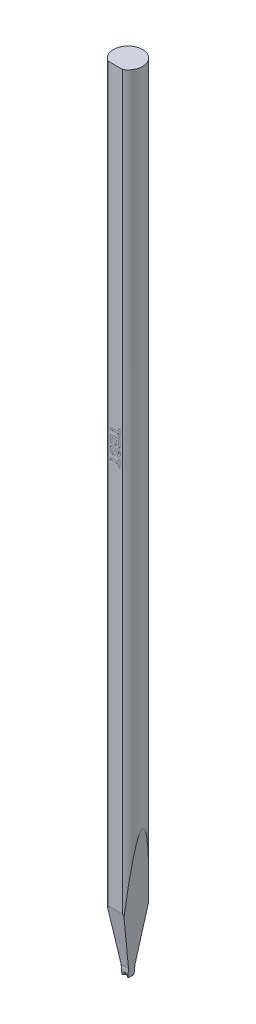
SolidWorks part; units mm, degrees
ref_plane "Ebene vorne" through (0, 0, 0) normal (0, 0, 1) x (1, 0, 0)
ref_plane "Ebene oben" through (0, 0, 0) normal (0, 1, 0) x (1, 0, 0)
ref_plane "Ebene rechts" through (0, 0, 0) normal (1, 0, 0) x (0, 0, -1)
sketch "sketch_TL_cutting" plane through (0, 0, 0) normal (0, 1, 0) x (1, 0, 0)
  circle A0 centre (0, 0) radius 1.4986
extrude "TL_cutting" add sketch "sketch_TL_cutting" along normal blind 81.28
sketch "sketch_TDF_grinding" plane through (0, 0, 0) normal (0, 1, 0) x (1, 0, 0)
  line L0 (0, 0) -> (0, -1.2954) construction
  line L1 (-1.5086, -4.3126) -> (1.5086, -4.3126)
  line L2 (-1.5086, -4.3126) -> (-1.5086, -1.2954)
  line L3 (-1.5086, -1.2954) -> (1.5086, -1.2954)
  line L4 (1.5086, -4.3126) -> (1.5086, -1.2954)
  circle A1 centre (0, 0) radius 1.4986 construction
  point P9 (0, -4.3126)
  dimension "TD_2Offset_X" = 3.0172
  dimension "TD_2Offset_Z" = 3.0172
extrude "TDF_grinding" cut sketch "sketch_TDF_grinding" along normal through all
sketch "sketch_engraving" plane through (0, 0, 1.2954) normal (0, 0, 1) x (1, 0, 0)
  line L0 (0.7535, 81.28) -> (-0.7535, 81.28) construction
  line L6 (-0.7535, 0) -> (0.7535, 0) construction
  line L7 (0, 0) -> (0, 49.28) construction
  line L8 (-0.5, 49.28) -> (-0.5, 0) construction
  text T0 "TEST" font "Arial" height 1
  dimension "D2" = 0.5
  dimension "EngravingStart" = 32
extrude "engraving" cut sketch "sketch_engraving" against normal blind 0.005
sketch "sketch_VW_VR_grinding" plane through (0, 0, 0) normal (0, 0, 1) x (1, 0, 0)
  line L0 (-1.4936, -0.01) -> (-1.4936, 0.874)
  line L1 (1.4936, -0.01) -> (1.4936, 0.874)
  line L2 (-1.4936, 0) -> (1.4936, 0) construction
  line L3 (-1.5086, 0.879) -> (-1.4986, 0.879)
  line L4 (1.4986, 0.879) -> (1.5086, 0.879)
  line L5 (-1.5086, 0.879) -> (-1.5086, -0.01)
  line L6 (-1.5086, -0.01) -> (-1.4936, -0.01)
  line L7 (1.4936, -0.01) -> (1.5086, -0.01)
  line L8 (1.5086, -0.01) -> (1.5086, 0.879)
  line L9 (-1.4986, 0.879) -> (-1.4986, 0.874) construction
  line L10 (-1.4936, 0.874) -> (-1.4986, 0.874) construction
  line L11 (1.4936, 0.874) -> (1.4986, 0.874) construction
  line L12 (1.4986, 0.879) -> (1.4986, 0.874) construction
  arc A0 (-1.4986, 0.879) -> (-1.4936, 0.874) centre (-1.4986, 0.874) cw
  arc A2 (1.4936, 0.874) -> (1.4986, 0.879) centre (1.4986, 0.874) cw
  dimension "D1" = 0.01
  dimension "D4" = 3.0172
extrude "VW_VR_grinding" cut sketch "sketch_VW_VR_grinding" against normal blind 1.5086 and the other way blind 1.5086
sketch "sketch_ISA_grinding" plane through (0, 0, 0) normal (0, 0, 1) x (1, 0, 0)
  line L0 (-0.2997, 0) -> (-1.5086, 13.8176)
  line L4 (1.5086, 13.8176) -> (0.2997, 0)
  line L5 (0.2997, 0) -> (-0.2997, 0)
  line L6 (0, 0) -> (0, 30.49) construction
  line L7 (-1.5086, 13.8176) -> (-1.5086, -0.01)
  line L12 (-1.5086, -0.01) -> (1.5086, -0.01)
  line L13 (1.5086, -0.01) -> (1.5086, 13.8176)
  dimension "ISA" = 10
  dimension "TD_2Offset" = 3.0172
  dimension "Offset" = 0.01
extrude "ISA_grinding" cut sketch "sketch_ISA_grinding" against normal blind 1.5086 and the other way blind 1.5086
sketch "sketch_pre_FRX_BRX" plane through (0, 0, 0) normal (1, 0, 0) x (0, 0, -1)
  line L0 (1.4986, -0.01) -> (1.4986, 3.9152) construction
  line L1 (-1.2954, -0.01) -> (-1.2954, 0.879) construction
  line L2 (-0.3251, -0.01) -> (-0.3251, 0.879)
  line L3 (-0.3251, 0.879) -> (-1.5086, 0.879)
  line L4 (-1.5086, 0.879) -> (-1.5086, -0.01)
  line L5 (-1.5086, -0.01) -> (-0.3251, -0.01)
  line L6 (0.3251, -0.01) -> (0.3251, 0.879)
  line L7 (0.3251, 0.879) -> (1.5086, 0.879)
  line L8 (1.5086, 0.879) -> (1.5086, -0.01)
  line L9 (1.5086, -0.01) -> (0.3251, -0.01)
  dimension "D3" = 0.01
  dimension "D4" = 0.889
  dimension "D5" = 3.0172
  dimension "D6" = 0.6502
  dimension "D2" = 0.01
  dimension "D7" = 1.8237
extrude "pre_FRX_BRX" cut sketch "sketch_pre_FRX_BRX" against normal blind 1.5086 and the other way blind 1.5086
sketch "sketch_contour_V-Groove" plane through (0, 0, 0) normal (1, 0, 0) x (0, 0, -1)
  line L0 (-1.2954, 0.1905) -> (0, 0.1905)
  line L1 (0, 0.1905) -> (1.4986, 0.1905)
  line L2 (1.4986, -0.8411) -> (1.4986, 1.3178) construction
  line L3 (-1.2954, -0.9209) -> (-1.2954, 1.9363) construction
  line L4 (-1.2954, 0) -> (1.4986, 0) construction
  line L5 (0.3251, 0) -> (0.3251, 0.1905) construction
  line L6 (-0.3251, 0) -> (-0.3251, 0.1905) construction
  dimension "D1" = 0
ref_plane "front" through (0, 0, 1.2954) normal (0, 0, 1) x (1, 0, 0)
ref_plane "back" through (0, 0, -1.4986) normal (0, 0, 1) x (1, 0, 0)
sketch "sketch_section_V-Groove" plane through (0, 0, 1.2954) normal (0, 0, 1) x (1, 0, 0)
  line L0 (-1.499, -1.905) -> (-0.0499, 0.1645)
  line L2 (0.0499, 0.1645) -> (1.499, -1.905)
  line L3 (-1.499, -1.905) -> (1.499, -1.905)
  line L4 (0, -1.905) -> (0, 0.1905) construction
  line L5 (-0.1651, 0) -> (0.1651, 0) construction
  line L6 (-0.2997, 0) -> (0.2997, 0) construction
  arc A0 (0.0499, 0.1645) -> (-0.0499, 0.1645) centre (0, 0.1296) ccw
  point P5 (0, 0)
  point P9 (0, 0)
  point P14 (0, 0)
  point P15 (0, 0)
  point P16 (0, 0)
  point P17 (0, 0)
  dimension "GA" = 70
sweep "V-Groove_EDM" cut profiles "sketch_section_V-Groove" path "sketch_contour_V-Groove"
fillet "FR_EDM" radius 0.2261 3 edges at (0.1075, 0.0823, 0.3251) (0, 0.1905, 0.3251) (-0.1075, 0.0823, 0.3251)
fillet "BR_EDM" radius 0.2261 3 edges at (0.1075, 0.0823, -0.3251) (0, 0.1905, -0.3251) (-0.1075, 0.0823, -0.3251)
sketch "sketch_FA_BA_grinding" plane through (0, 0, 0) normal (1, 0, 0) x (0, 0, -1)
  line L2 (2.4986, 13.2154) -> (2.4986, -0.1)
  line L3 (2.4986, -0.1) -> (0.3251, -0.1)
  line L5 (0.3251, -0.1) -> (0.3251, 0.889)
  line L6 (0.3251, 0.889) -> (2.4986, 13.2154)
  line L7 (1.4986, -0.1) -> (1.4986, 7.5441) construction
  line L8 (-1.2954, 6.3917) -> (-1.2954, -0.1) construction
  line L9 (-4.003, 21.7474) -> (-0.3251, 0.889)
  line L10 (-0.3251, 0.889) -> (-0.3251, -0.1)
  line L11 (-0.3251, -0.1) -> (-4.003, -0.1)
  line L12 (-4.003, -0.1) -> (-4.003, 21.7474)
  line L13 (-0.3251, 0.889) -> (0.3251, 0.889) construction
  dimension "D4" = 1
  dimension "D1" = 0.1
  dimension "FA" = 10
  dimension "BA" = 10
extrude "FA_BA_grinding" cut sketch "sketch_FA_BA_grinding" against normal blind 1.5086 and the other way blind 1.5086
sketch "sketch_groove_dimensions" plane through (0, 0, 0) normal (1, 0, 0) x (0, 0, -1)
  line L0 (-0.0991, 0.1905) -> (0.0991, 0.1905)
  line L1 (-0.3251, 0) -> (-0.3251, 0.4166) construction
  line L2 (1.4986, 0) -> (1.4986, 0.4166) construction
  line L3 (0.3251, 0) -> (0.3251, 0.4166) construction
  line L4 (-1.2954, 0) -> (-1.2954, 0.3999) construction
  arc A0 (0.0991, 0.1905) -> (0.3251, 0.4166) centre (0.0991, 0.4166) ccw
  arc A1 (-0.0991, 0.1905) -> (-0.3251, 0.4166) centre (-0.0991, 0.4166) cw
equation "\"_Offset\"=0.01mm"
equation "\"TL\"=81.28mm"
equation "\"TD\"=2.9972mm"
equation "\"TDF\"=2.794mm"
equation "\"BA\"=10deg"
equation "\"ISA\"=10deg"
equation "\"FA\"=10deg"
equation "\"GR\"=0.06096mm"
equation "\"GA\"=70deg"
equation "\"GD\"=0.1905mm"
equation "\"FL\"=0.65024mm"
equation "\"F\"=0.35052mm"
equation "\"FX\"=0mm"
equation "\"B\"=0.3302mm"
equation "\"VW\"=0mm"
equation "\"cleaned_VR\"= IIF ( \"VR\" > 0 , \"VR\" , \"E\" - \"_Offset\" )"
equation "\"cleaned_VW\"= IIF ( \"VW\" > 0 , \"VW\" , \"TD\" - \"_Offset\" )"
equation "\"back_edge\"= \"TD\" / 2 - \"X\""
equation "\"side_edge_Offset\"= \"TD\" / 2 + \"_Offset\""
equation "\"TD@sketch_TL_cutting\"=\"TD\""
equation "\"TL@TL_cutting\"=\"TL\""
equation "\"TDF@sketch_TDF_grinding\"=\"TDF\""
equation "\"TD_2Offset_X@sketch_TDF_grinding\"=\"TD\"+2*\"_Offset\""
equation "\"TD_2Offset_Z@sketch_TDF_grinding\"=\"TD\"+2*\"_Offset\""
equation "\"TL_Offset\"= \"TL\" + \"_Offset\""
equation "\"ISA@sketch_ISA_grinding\"=\"ISA\""
equation "\"W@sketch_ISA_grinding\"=\"W\""
equation "\"TD_2Offset@sketch_ISA_grinding\"=\"TD\"+2*\"_Offset\""
equation "\"Offset@sketch_ISA_grinding\"=\"_Offset\""
equation "\"05TD_Offset_posZ@ISA_grinding\"=\"side_edge_Offset\""
equation "\"05TD_Offset_negZ@ISA_grinding\"=\"side_edge_Offset\""
equation "\"E\"=0.889mm"
equation "\"cleaned_X\"= IIF ( \"X\" > 0 , \"X\" , \"TD\" / 2 - \"FL\" / 2 )"
equation "\"FR\"=0.22606mm"
equation "\"BR\"=0.22606mm"
equation "\"D1\"= \"side_edge_Offset\""
equation "\"D2\"= \"side_edge_Offset\""
equation "\"TDF@sketch_FA_BA_grinding\" = \"TDF\""
equation "\"FL@sketch_FA_BA_grinding\"=\"FL\""
equation "\"E@sketch_FA_BA_grinding\" = \"E\""
equation "\"D1@FA_BA_grinding\"=\"side_edge_Offset\""
equation "\"D2@FA_BA_grinding\"=\"side_angle_Offset\""
equation "\"10GD@sketch_section_V-Groove\" = 10 * \"GD\""
equation "\"GA@sketch_section_V-Groove\" = \"GA\""
equation "\"B@sketch_section_V-Groove\" = \"B\""
equation "\"GD@sketch_contour_V-Groove\" = \"GD\""
equation "\"cleaned_FRX\"= IIF ( \"FRX\" > 0 , \"FRX\" , \"FR\" )"
equation "\"cleaned_BRX\"= IIF ( \"BRX\" > 0 , \"BRX\" , \"BR\" )"
equation "\"FL_groove_angle\"=0deg"
equation "\"D3@sketch_pre_FRX_BRX\" = \"_Offset\""
equation "\"D4@sketch_pre_FRX_BRX\" = \"E\""
equation "\"D5@sketch_pre_FRX_BRX\" = 2 * \"side_edge_Offset\""
equation "\"D6@sketch_pre_FRX_BRX\" = \"FL\" + ( \"FR\" - \"cleaned_FRX\" ) + ( \"BR\" - \"cleaned_BRX\" )"
equation "\"TD/2@sketch_pre_FRX_BRX\" = \"TD\" / 2"
equation "\"TDF@sketch_pre_FRX_BRX\" = \"TDF\""
equation "\"D2@sketch_pre_FRX_BRX\" = \"_Offset\""
equation "\"D1@pre_FRX_BRX\" = \"side_edge_Offset\""
equation "\"D2@pre_FRX_BRX\" = \"side_edge_Offset\""
equation "\"D1@BR_EDM\"=\"BR\""
equation "\"TD/2@sketch_FA_BA_grinding\" = \"TD\" / 2"
equation "\"TD/2@sketch_contour_V-Groove\" = \"TD\" / 2"
equation "\"TDF@sketch_contour_V-Groove\" = \"TDF\""
equation "\"D1@sketch_contour_V-Groove\"=\"FL_groove_angle\""
equation "\"FL@sketch_contour_V-Groove\"=\"FL\""
equation "\"FL/2@sketch_contour_V-Groove\" = \"FL\" / 2"
equation "\"D1@FR_EDM\"=\"FR\""
equation "\"D1@sketch_VW_VR_grinding\" = \"_Offset\""
equation "\"D4@sketch_VW_VR_grinding\" = 2 * \"side_edge_Offset\""
equation "\"VR@sketch_VW_VR_grinding\" = \"cleaned_VR\""
equation "\"VW@sketch_VW_VR_grinding\"=\"cleaned_VW\""
equation "\"D1@VW_VR_grinding\" = \"side_edge_Offset\""
equation "\"D2@VW_VR_grinding\" = \"side_edge_Offset\""
equation "\"X\"=0mm"
equation "\"VR\"=0mm"
equation "\"W\"=0.59944mm"
equation "\"VW_radius\"= \"cleaned_VW\" / 10"
equation "\"VW_radius_cleaned\"= IIF ( \"VW\" > 0 , \"VW_radius\" , \"_Offset\" / 2 )"
equation "\"D2@sketch_VW_VR_grinding\"=\"VW_radius_cleaned\""
equation "\"FRX\"=0mm"
equation "\"BRX\"=0mm"
equation "\"FA@sketch_FA_BA_grinding\" = \"FA\""
equation "\"D4@sketch_FA_BA_grinding\"=\"_Offset\"*100"
equation "\"BA@sketch_FA_BA_grinding\" = \"BA\""
equation "\"D1@sketch_groove_dimensions\" = \"TD\" / 2"
equation "\"FL@sketch_groove_dimensions\" = \"FL\""
equation "\"FR@sketch_groove_dimensions\" = \"FR\""
equation "\"BR@sketch_groove_dimensions\" = \"BR\""
equation "\"FRX@sketch_groove_dimensions\" = \"cleaned_FRX\""
equation "\"BRX@sketch_groove_dimensions\" = \"cleaned_BRX\""
equation "\"GD@sketch_groove_dimensions\" = \"GD\""
equation "\"cleaned_FX\"= IIF ( \"FX\" > 0 , \"FX\" , \"TDF\" - ( \"TD\" + \"FL\" ) / 2 )"
equation "\"D7@sketch_pre_FRX_BRX\"=\"TDF\"-\"cleaned_FX\"-(\"FR\"-\"cleaned_FRX\")"
equation "\"FX@sketch_contour_V-Groove\" = \"cleaned_FX\""
equation "\"FX@sketch_FA_BA_grinding\" = \"cleaned_FX\""
equation "\"TDF@sketch_groove_dimensions\" = \"TDF\""
equation "\"FX@sketch_groove_dimensions\" = \"cleaned_FX\""
equation "\"EngravingStart\" =32mm"
equation "\"EngravingStart@sketch_engraving\" = \"EngravingStart\""
